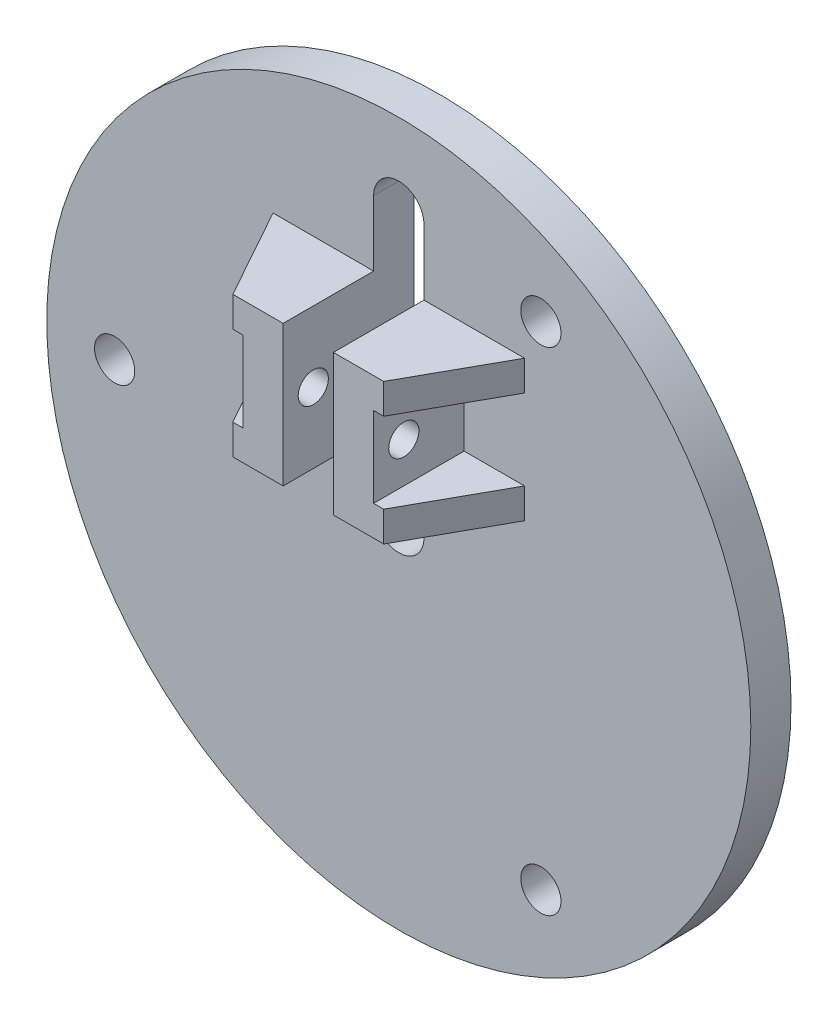
SolidWorks part; units mm, degrees
material "1060 合金"
ref_plane "前视基准面" through (0, 0, 0) normal (0, 0, 1) x (1, 0, 0)
ref_plane "上视基准面" through (0, 0, 0) normal (0, 1, 0) x (1, 0, 0)
ref_plane "右视基准面" through (0, 0, 0) normal (1, 0, 0) x (0, 0, -1)
sketch "草图1" plane through (0, 0, 0) normal (0, 0, 1) x (1, 0, 0)
  line L0 (0, 0) -> (0, 27) construction
  line L1 (-2.5, 0) -> (-2.5, 27)
  line L2 (2.5, 0) -> (2.5, 27)
  circle A0 centre (0, 0) radius 35
  circle A1 centre (14.125, 24.4652) radius 2
  arc A2 (-2.5, 0) -> (2.5, 0) centre (0, 0) ccw
  arc A3 (2.5, 27) -> (-2.5, 27) centre (0, 27) ccw
  circle A4 centre (14.125, -24.4652) radius 2
  circle A5 centre (-28.25, 0) radius 2
  point P4 (0, 13.5)
  dimension "D1" = 70
  dimension "D2" = 28.25
  dimension "D5" = 4
  dimension "D6" = 0
  dimension "D3" = 3
  dimension "D4" = 27
extrude "凸台-拉伸1" add sketch "草图1" along normal blind 4
sketch "草图2" plane through (0, 0, 4) normal (0, 0, 1) x (1, 0, 0)
  line L0 (-2.5, 13.5) -> (-2.5, 20.5)
  line L1 (-2.5, 27) -> (-2.5, 0) construction
  line L2 (-2.5, 20.5) -> (-12.5, 20.5)
  line L3 (-12.5, 20.5) -> (-12.5, 17.5)
  line L4 (-12.5, 17.5) -> (-6.5, 17.5)
  line L5 (-6.5, 17.5) -> (-6.5, 9.5)
  line L6 (-6.5, 9.5) -> (-12.5, 9.5)
  line L7 (-12.5, 9.5) -> (-12.5, 6.5)
  line L8 (-12.5, 6.5) -> (-2.5, 6.5)
  line L9 (-2.5, 6.5) -> (-2.5, 13.5)
  line L10 (0, 0) -> (0, 33.3427) construction
  line L11 (2.5, 6.5) -> (2.5, 13.5)
  line L12 (12.5, 6.5) -> (2.5, 6.5)
  line L13 (12.5, 9.5) -> (12.5, 6.5)
  line L14 (6.5, 9.5) -> (12.5, 9.5)
  line L15 (6.5, 17.5) -> (6.5, 9.5)
  line L16 (12.5, 17.5) -> (6.5, 17.5)
  line L17 (12.5, 20.5) -> (12.5, 17.5)
  line L18 (2.5, 20.5) -> (12.5, 20.5)
  line L19 (2.5, 13.5) -> (2.5, 20.5)
  dimension "D1" = 10
  dimension "D2" = 4
  dimension "D3" = 3
  dimension "D4" = 3
  dimension "D5" = 7
  dimension "D6" = 7
  dimension "D7" = 10
extrude "凸台-拉伸2" add sketch "草图2" along normal blind 9
sketch "草图3" plane through (0, 6.5, 0) normal (0, -1, 0) x (1, 0, 0)
  line L0 (-12.5, 4) -> (-12.5, 13)
  line L1 (-12.5, 13) -> (-7.5, 13)
  line L2 (-12.5, 13) -> (-2.5, 13) construction
  line L3 (-7.5, 13) -> (-12.5, 4)
  line L4 (12.5, 4) -> (12.5, 13)
  line L5 (12.5, 13) -> (7.5, 13)
  line L6 (2.5, 13) -> (12.5, 13) construction
  line L7 (7.5, 13) -> (12.5, 4)
extrude "切除-拉伸1" cut sketch "草图3" against normal up to surface (14 mm away) up to face at (-6.25, 20.5, 9.625)
sketch "草图4" plane through (-6.5, 0, 0) normal (-1, 0, 0) x (0, 0, 1)
  circle A0 centre (10, 13.5) radius 1.45
extrude "切除-拉伸2" cut sketch "草图4" against normal up to surface (13 mm away) up to face at (6.5, 13.5, 8.5)
sketch "草图5" plane through (6.5, 0, 0) normal (1, 0, 0) x (0, 0, -1)
  circle A0 centre (-10, 13.5) radius 1.5
  dimension "D1" = 3
extrude "切除-拉伸3" cut sketch "草图5" against normal up to surface (13 mm away) up to face at (-6.5, 12.05, 10)
